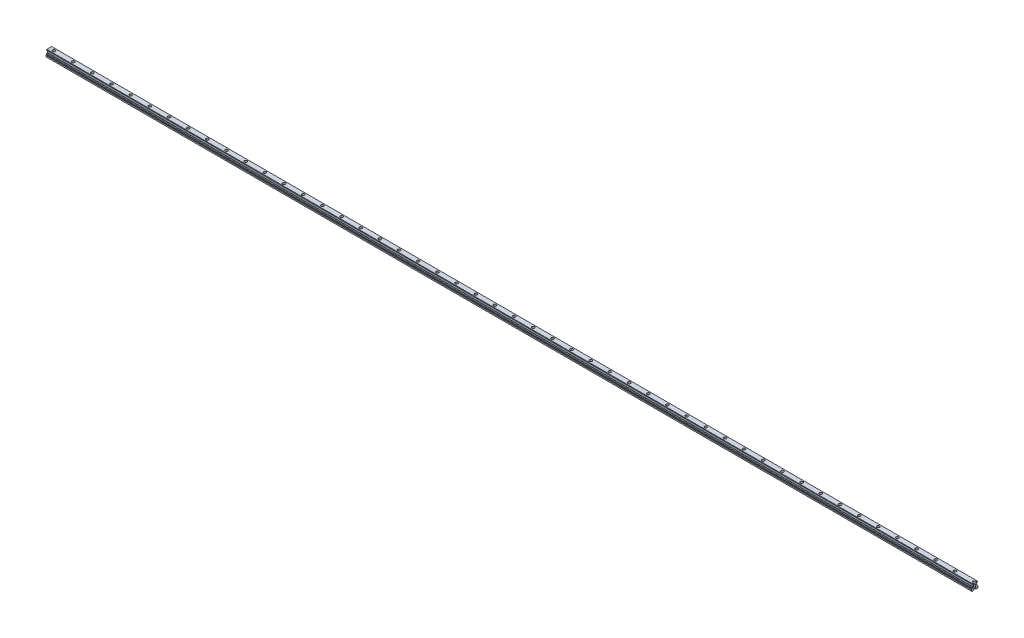
SolidWorks part; units mm, degrees
ref_plane "Front Plane" through (0, 0, 0) normal (0, 0, 1) x (1, 0, 0)
ref_plane "Top Plane" through (0, 0, 0) normal (0, 1, 0) x (1, 0, 0)
ref_plane "Right Plane" through (0, 0, 0) normal (1, 0, 0) x (0, 0, -1)
ref_plane "Plane1" through (58.5, 0, 0) normal (1, 0, 0) x (0, 0, -1)
sketch "Sketch7" plane through (58.5, 0, 0) normal (1, 0, 0) x (0, 0, -1)
  line L30 (-7.709, 8.8831) -> (-8.5, 8.6011)
  line L32 (-8.75, 5.6717) -> (-10, 4.95)
  line L35 (-10, 4.95) -> (-10, 1)
  line L37 (-10, 1) -> (-9, 0)
  line L39 (-4, 0) -> (-3.5, 0.5)
  line L42 (-3.5, 0.5) -> (3.5, 0.5)
  line L48 (3.5, 0.5) -> (4, 0)
  line L52 (4, 0) -> (9, 0)
  line L57 (-8.5, 8.6011) -> (-8.5, 6.1047)
  line L61 (-9, 0) -> (-4, 0)
  line L69 (8.5, 6.1047) -> (8.5, 8.4669)
  line L71 (6.5033, 10.3667) -> (6, 10.87)
  line L72 (6, 10.87) -> (6, 14.93)
  line L73 (6, 14.93) -> (6.5033, 15.4333)
  line L75 (8.5, 17.1989) -> (8.5, 19.3)
  line L77 (7.5, 20.3) -> (-7.5, 20.3)
  line L79 (-8.5, 19.3) -> (-8.5, 17.3331)
  line L81 (-6.5033, 15.4333) -> (-6, 14.93)
  line L82 (-6, 14.93) -> (-6, 10.87)
  line L83 (-6, 10.87) -> (-6.5033, 10.3667)
  line L85 (9, 0) -> (10, 1)
  line L87 (10, 1) -> (10, 4.95)
  line L89 (10, 4.95) -> (8.75, 5.6717)
  line L91 (8.5, 8.4669) -> (8.0847, 8.8822)
  line L93 (7.709, 16.9169) -> (8.5, 17.1989)
  line L95 (8.5, 19.3) -> (7.5, 20.3)
  line L97 (-7.5, 20.3) -> (-8.5, 19.3)
  line L99 (-8.5, 17.3331) -> (-8.0847, 16.9178)
  arc A8 (-8.75, 5.6717) -> (-8.5, 6.1047) centre (-9, 6.1047) ccw
  arc A12 (-7.709, 8.8831) -> (-6.5033, 10.3667) centre (-7.9, 10.27) ccw
  arc A15 (6.5033, 10.3667) -> (8.0847, 8.8822) centre (7.9, 10.27) ccw
  arc A16 (7.709, 16.9169) -> (6.5033, 15.4333) centre (7.9, 15.53) ccw
  arc A17 (-6.5033, 15.4333) -> (-8.0847, 16.9178) centre (-7.9, 15.53) ccw
  arc A19 (8.5, 6.1047) -> (8.75, 5.6717) centre (9, 6.1047) ccw
sketch "Sketch1" [suppressed] plane through (58.5, 0, 0) normal (1, 0, 0) x (0, 0, -1)
  line L0 (-8.5, 0) -> (8.5, 0)
  line L1 (8.5, 0) -> (8.5, 9.0051)
  line L2 (6.5033, 10.3667) -> (6, 10.87)
  line L3 (6, 10.87) -> (6, 14.93)
  line L4 (6, 14.93) -> (6.5033, 15.4333)
  line L5 (8.5, 16.7949) -> (8.5, 20.3)
  line L6 (8.5, 20.3) -> (-8.5, 20.3)
  line L7 (-8.5, 20.3) -> (-8.5, 16.7949)
  line L8 (-6.5033, 15.4333) -> (-6, 14.93)
  line L9 (-6, 14.93) -> (-6, 10.87)
  line L10 (-6, 10.87) -> (-6.5033, 10.3667)
  line L11 (-8.5, 9.0051) -> (-8.5, 0)
  arc A0 (8.5, 9.0051) -> (6.5033, 10.3667) centre (7.9, 10.27) cw
  arc A1 (6.5033, 15.4333) -> (8.5, 16.7949) centre (7.9, 15.53) cw
  arc A2 (-8.5, 16.7949) -> (-6.5033, 15.4333) centre (-7.9, 15.53) cw
  arc A3 (-6.5033, 10.3667) -> (-8.5, 9.0051) centre (-7.9, 10.27) cw
extrude "Boss-Extrude5" add sketch "Sketch7" along normal blind 2897
sketch "Sketch8" plane through (0, 20.3, 0) normal (0, 1, 0) x (1, 0, 0)
  line L0 (63.3132, 7.5) -> (63.3132, -7.5) construction
  line L1 (2955.5, 7.5) -> (58.5, 7.5) construction
  line L2 (2955.5, -7.5) -> (58.5, -7.5) construction
  line L3 (58.5, 0) -> (135.5743, 0) construction
  line L4 (58.5, -55) -> (58.5, 55) construction
  circle A0 centre (73.4716, 0) radius 4.25
  dimension "D1" = 8.5
extrude "Cut-Extrude1" cut sketch "Sketch8" against normal blind 9
sketch "Sketch9" plane through (0, 11.3, 0) normal (0, 1, 0) x (1, 0, 0)
  circle A0 centre (73.4716, 0) radius 3
  dimension "D1" = 6
extrude "Cut-Extrude2" cut sketch "Sketch9" against normal blind 17
pattern_linear "LPattern1" count 50 spacing 60 along (1, 0, 0) of "Cut-Extrude1", "Cut-Extrude2"
